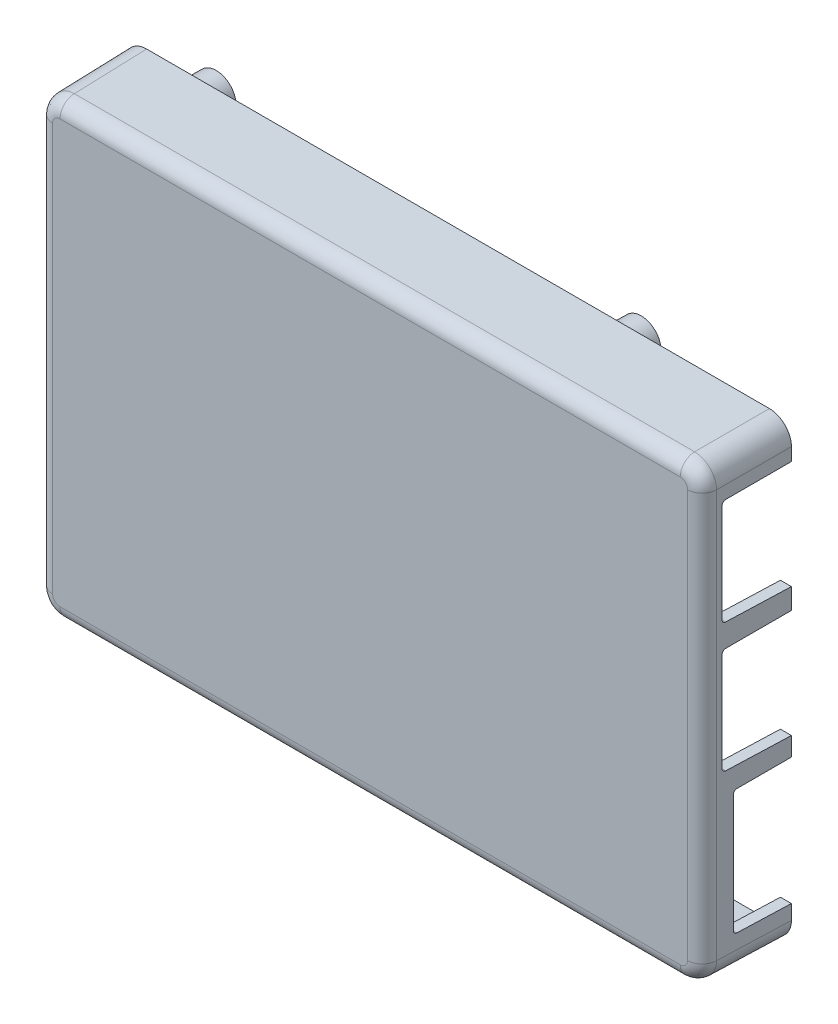
SolidWorks part; units mm, degrees
ref_plane "Front" through (0, 0, 0) normal (0, 0, 1) x (1, 0, 0)
ref_plane "Top" through (0, 0, 0) normal (0, 1, 0) x (1, 0, 0)
ref_plane "Right" through (0, 0, 0) normal (1, 0, 0) x (0, 0, -1)
sketch "Sketch1" plane through (0, 0, 0) normal (0, 0, 1) x (1, 0, 0)
  line L4 (-45.5, 31) -> (-45.5, -31)
  line L5 (-45.5, -31) -> (45.5, -31)
  line L6 (45.5, -31) -> (45.5, 31)
  line L7 (45.5, 31) -> (-45.5, 31)
  line L8 (-45.5, 31) -> (-45.5, -31)
  line L9 (-45.5, -31) -> (45.5, -31)
  line L10 (45.5, -31) -> (45.5, 31)
  line L11 (45.5, 31) -> (-45.5, 31)
  line L12 (-44, 29.5) -> (-44, -29.5)
  line L13 (-44, -29.5) -> (44, -29.5)
  line L14 (44, -29.5) -> (44, 29.5)
  line L15 (44, 29.5) -> (-44, 29.5)
  line L16 (-44, 29.5) -> (-44, -29.5)
  line L17 (-44, -29.5) -> (44, -29.5)
  line L18 (44, -29.5) -> (44, 29.5)
  line L19 (44, 29.5) -> (-44, 29.5)
  dimension "D1" = 0
  dimension "D2" = 0
extrude "Walls" add sketch "Sketch1" along normal blind 12
sketch "Sketch2" plane through (0, 0, 12) normal (0, 0, 1) x (1, 0, 0)
  line L4 (45.5, 31) -> (-45.5, 31)
  line L5 (-45.5, 31) -> (-45.5, -31)
  line L6 (-45.5, -31) -> (45.5, -31)
  line L7 (45.5, -31) -> (45.5, 31)
  line L8 (45.5, 31) -> (-45.5, 31)
  line L9 (-45.5, 31) -> (-45.5, -31)
  line L10 (-45.5, -31) -> (45.5, -31)
  line L11 (45.5, -31) -> (45.5, 31)
  dimension "D1" = 0
extrude "Base" add sketch "Sketch2" against normal blind 1.5
sketch "Sketch3" plane through (0, 0, 10.5) normal (0, 0, -1) x (-1, 0, 0)
  circle A0 centre (39, -24.5) radius 3
  circle A1 centre (-19, -24.5) radius 3
  circle A2 centre (-19, 24.5) radius 3
  circle A3 centre (39, 24.5) radius 3
  dimension "D1" = 6
extrude "Standoffs" add sketch "Sketch3" along normal blind 16.5 draft 1
hole_wizard "M2x0.4 Tapped Hole1" positions "Sketch4" profile "Sketch5" tap size "M2x0.4" standard "ANSI Metric"
sketch "Sketch4" plane through (0, 0, -6) normal (0, 0, -1) x (-1, 0, 0)
  point P0 (39, -24.5)
  point P3 (-19, -24.5)
  point P6 (-19, 24.5)
  point P9 (39, 24.5)
sketch "Sketch5" plane through (-39, -24.5, -6) normal (1, 0, 0) x (0, 1, 0)
  line L0 (0, 0) -> (0, 5.4807)
  line L1 (0, 5.4807) -> (0.8, 5)
  line L2 (0.8, 5) -> (0.8, 0)
  line L5 (0.8, 0) -> (0, 0)
  line L10 (0, 5.4807) -> (-0.8, 5) construction
  line L11 (0, -6.35) -> (0, 107.95) construction
  dimension "Tap Drill Dia." = 1.6
  dimension "Tap Drill Depth" = 5
  dimension "Drill Angle" = 118
cosmetic thread "Hole Thread1" parameters "D1"=4, "D2"=2
cosmetic thread "Hole Thread2" parameters "D1"=4, "D2"=2
cosmetic thread "Hole Thread3" parameters "D1"=4, "D2"=2
cosmetic thread "Hole Thread4" parameters "D1"=4, "D2"=2
sketch "Sketch6" plane through (0, 0, 0) normal (1, 0, 0) x (0, 0, -1)
  line L0 (5.9, -17.348) -> (-7.3, -17.348) construction
  line L1 (5.9, -19.848) -> (5.9, -14.848) construction
  line L2 (-7.3, -25.248) -> (-7.3, -9.448) construction
  line L3 (3.0235, -25.5) -> (5.6315, -25.5) construction
  line L4 (-7.8, -8.696) -> (6.4, -8.696)
  line L5 (-7.8, -8.696) -> (-7.8, -26)
  line L6 (-7.8, -26) -> (6.4, -26)
  line L7 (6.4, -8.696) -> (6.4, -26)
  line L8 (-7.8, -8.696) -> (6.4, -26) construction
  line L9 (-7.8, -26) -> (6.4, -8.696) construction
  line L10 (5.9, -25.248) -> (5.9, -24.4366) construction
  line L11 (-8.8, 1.25) -> (6.69, 1.25) construction
  line L12 (-8.8, 7.5) -> (-8.8, -5) construction
  line L13 (6.69, 7.74) -> (6.69, -5.24) construction
  line L14 (-8.25, 8.14) -> (6.69, 8.14) construction
  line L15 (-9.3, -6.14) -> (7.19, -6.14)
  line L16 (-9.3, -6.14) -> (-9.3, 8.64)
  line L17 (-9.3, 8.64) -> (7.19, 8.64)
  line L18 (7.19, -6.14) -> (7.19, 8.64)
  line L19 (-9.3, -6.14) -> (7.19, 8.64) construction
  line L20 (-9.3, 8.64) -> (7.19, -6.14) construction
  line L21 (-9.3, 11.46) -> (7.19, 11.46)
  line L22 (-9.3, 11.46) -> (-9.3, 26.24)
  line L23 (-9.3, 26.24) -> (7.19, 26.24)
  line L24 (7.19, 11.46) -> (7.19, 26.24)
  line L25 (-8.8, 18.85) -> (6.69, 18.85) construction
  line L26 (-9.3, 11.46) -> (7.19, 26.24) construction
  line L27 (-9.3, 26.24) -> (7.19, 11.46) construction
  line L28 (-8.8, 25.1) -> (-8.8, 12.6) construction
  point P6 (-0.7, -17.348)
  point P21 (-1.055, 1.25)
  point P30 (-8.8, 18.85)
  point P33 (-1.055, 18.85)
  dimension "D1" = 0.5
  dimension "D2" = 0.5
  dimension "D3" = 0.5
  dimension "D4" = 0.5
  dimension "D5" = 2
extrude "USB and Ethernet Ports " cut sketch "Sketch6" along normal through all from offset 30
draft "Draft1" type of draft neutral plane draft angle 1 faces to draft 4 face at (45.5, 0.688, 4.8) face at (0, -31, 6) face at (-45.5, 0, 6) face at (0, 31, 6) neutral plane through (0, 0, 0) neutral plane normal (0, 0, -1) reverse direction yes parameters "D1"=1
draft "Draft2" type of draft neutral plane draft angle 1 faces to draft 4 face at (44, 0.688, 4.6125) face at (0, -29.5, 5.25) face at (-44, 0, 5.25) face at (0, 29.5, 5.25) neutral plane through (0, 0, 0) neutral plane normal (0, 0, -1) parameters "D1"=1
fillet "Fillet1" radius 3 4 edges at (-45.3953, 30.8953, 6) (45.3953, -30.8953, 6) (45.3953, 30.8953, 6) (-45.3953, -30.8953, 6)
fillet "Fillet2" radius 1.5 4 edges at (-43.9084, 29.4084, 5.25) (43.9084, -29.4084, 5.25) (43.9084, 29.4084, 5.25) (-43.9084, -29.4084, 5.25)
fillet "Fillet3" radius 2 8 edges at (44.412, 29.912, 12) (45.2905, 0, 12) (44.412, -29.912, 12) (0, -30.7905, 12) (-44.412, -29.912, 12) (-45.2905, 0, 12) (-44.412, 29.912, 12) (0, 30.7905, 12)
fillet "Fillet4" radius 0.5 12 edges at (-43.3775, -28.8775, 10.5) (0, -29.3167, 10.5) (43.3775, -28.8775, 10.5) (43.8167, 0, 10.5) (43.3775, 28.8775, 10.5) (0, 29.3167, 10.5) (-43.3775, 28.8775, 10.5) (-43.8167, 0, 10.5) (-36, -24.5, 10.5) (22, -24.5, 10.5) (22, 24.5, 10.5) (-36, 24.5, 10.5)
draft "Draft3" type of draft neutral plane draft angle 1 faces to draft 6 face at (44.6819, -26, 3.9) face at (44.6688, 11.46, 4.65) face at (44.6688, -6.14, 4.65) face at (44.6819, -8.696, 3.9) face at (44.6688, 8.64, 4.65) face at (44.6688, 26.24, 4.65) neutral plane through (0, 0, 0) neutral plane normal (0, 0, -1) parameters "D1"=1
fillet "Fillet5" radius 0.5 6 edges at (44.5877, 11.6223, 9.3) (44.5877, -5.9777, 9.3) (44.6139, -25.8639, 7.8) (44.6139, -8.8321, 7.8) (44.5877, 8.4777, 9.3) (44.5877, 26.0777, 9.3)
